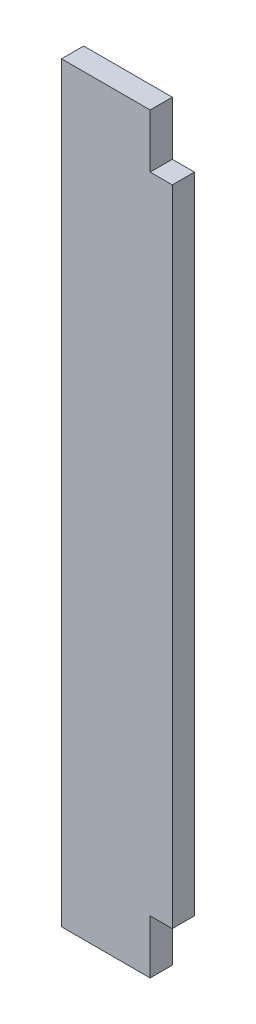
SolidWorks part; units mm, degrees
material "Pine"
ref_plane "Front Plane" through (0, 0, 0) normal (0, 0, 1) x (1, 0, 0)
ref_plane "Top Plane" through (0, 0, 0) normal (0, 1, 0) x (1, 0, 0)
ref_plane "Right Plane" through (0, 0, 0) normal (1, 0, 0) x (0, 0, -1)
sketch "Sketch1" plane through (0, 0, 0) normal (0, 0, 1) x (1, 0, 0)
  line L0 (8932.6508, -5243.5125) -> (10226.1458, -5243.5125)
  line L1 (9086.3208, -4722.0918) -> (10222.9708, -4853.7812)
  line L2 (8914.8708, -6342.0625) -> (10197.5708, -6342.0625)
  line L3 (8914.8708, -5808.6625) -> (10197.5708, -5808.6625)
  line L4 (8919.6333, -5253.0375) -> (10218.2083, -5253.0375)
  line L5 (9134.2633, -4656.1375) -> (9134.2633, -4638.3575)
  line L6 (9091.0833, -4638.3575) -> (9134.2633, -4638.3575)
  line L7 (9091.0833, -4567.2375) -> (9091.0833, -4638.3575)
  line L8 (9134.2633, -4656.1375) -> (9581.3033, -4656.1375)
  line L9 (9091.0833, -4567.2375) -> (9624.4833, -4567.2375)
  line L10 (9581.3033, -4656.1375) -> (9581.3033, -4638.3575)
  line L11 (9581.3033, -4638.3575) -> (9624.4833, -4638.3575)
  line L12 (9624.4833, -4567.2375) -> (9624.4833, -4638.3575)
  line L13 (8932.6508, -5225.7325) -> (9344.9775, -5225.7325)
  line L14 (8932.6508, -5256.2125) -> (8932.6508, -5243.5125)
  line L15 (8911.6958, -5256.2125) -> (8932.6508, -5256.2125)
  line L16 (8914.8708, -4722.0918) -> (9086.3208, -4722.0918)
  line L17 (8911.6958, -4715.5913) -> (8932.6508, -4715.5913)
  line L18 (8914.8708, -6342.0625) -> (8914.8708, -5808.6625)
  line L19 (12082.9917, -4722.0918) -> (10946.3417, -4853.7812)
  line L20 (12236.6617, -5243.5125) -> (10943.1667, -5243.5125)
  line L21 (10951.1042, -5253.0375) -> (12249.6792, -5253.0375)
  line L22 (10838.3917, -5656.2625) -> (11308.2917, -5656.2625)
  line L23 (10838.3917, -5719.7625) -> (11308.2917, -5719.7625)
  line L24 (10838.3917, -5742.5368) -> (11308.2917, -5742.5368)
  line L25 (10806.6417, -6342.0625) -> (11340.0417, -6342.0625)
  line L26 (10803.4667, -6335.7125) -> (11343.2167, -6335.7125)
  line L27 (10803.4667, -6317.9325) -> (11343.2167, -6317.9325)
  line L28 (10943.1667, -5225.7325) -> (11376.4483, -5225.7325)
  line L29 (11506.7292, -4754.5625) -> (10806.6417, -4827.5875)
  line L30 (11506.7292, -4567.2375) -> (11506.7292, -4754.5625)
  line L31 (10806.6417, -4567.2375) -> (10806.6417, -4827.5875)
  line L32 (10806.6417, -4567.2375) -> (11506.7292, -4567.2375)
  line L33 (10235.6708, -6329.3625) -> (10245.1958, -6329.3625)
  line L34 (10245.1958, -6329.3625) -> (10254.7208, -6278.5625)
  line L35 (10302.3458, -6329.3625) -> (10311.8708, -6278.5625)
  line L36 (10302.3458, -6329.3625) -> (10292.8208, -6329.3625)
  line L37 (10245.1958, -5821.3625) -> (10254.7208, -5872.1625)
  line L38 (10235.6708, -5821.3625) -> (10245.1958, -5821.3625)
  line L39 (10292.8208, -5821.3625) -> (10302.3458, -5821.3625)
  line L40 (10302.3458, -5821.3625) -> (10311.8708, -5872.1625)
  line L41 (10235.6708, -5821.3625) -> (10235.6708, -6329.3625)
  line L42 (10254.7208, -5872.1625) -> (10254.7208, -6278.5625)
  line L43 (10311.8708, -5872.1625) -> (10311.8708, -6278.5625)
  line L44 (10292.8208, -5821.3625) -> (10292.8208, -6329.3625)
  line L45 (8932.6508, -5225.7325) -> (8932.6508, -4715.5913)
  line L46 (8911.6958, -4715.5913) -> (8911.6958, -5256.2125)
  line L47 (8914.8708, -5248.275) -> (8914.8708, -4722.0918)
  line L48 (8919.6333, -5253.0375) -> (8914.8708, -5248.275)
  line L49 (8914.8708, -5145.0875) -> (8937.426, -5145.0875)
  line L50 (8914.8708, -5202.2375) -> (8937.426, -5202.2375)
  line L51 (10838.3917, -5656.2625) -> (10838.3917, -5719.7625)
  line L52 (10832.0417, -5736.1868) -> (10856.1717, -5736.1868)
  line L53 (10806.6417, -6342.0625) -> (10806.6417, -5818.7368)
  line L54 (10832.0417, -5649.9125) -> (10856.1717, -5649.9125)
  line L55 (10832.0417, -5726.1125) -> (10856.1717, -5726.1125)
  line L56 (10806.6417, -5818.7368) -> (10833.9015, -5818.7368)
  line L57 (10832.0417, -5806.0442) -> (10851.6815, -5806.0442)
  line L58 (10856.1717, -5801.5541) -> (10856.1717, -5736.1868)
  line L59 (10838.3917, -5814.2467) -> (10838.3917, -5742.5368)
  line L60 (10832.0417, -5806.0442) -> (10832.0417, -5736.1868)
  line L61 (10803.4667, -6317.9325) -> (10803.4667, -6335.7125)
  line L62 (10197.5708, -5808.6625) -> (10197.5708, -6342.0625)
  line L63 (9762.3842, -6348.4125) -> (9762.3842, -5802.3125)
  line L64 (9780.1642, -6348.4125) -> (9762.3842, -6348.4125)
  line L65 (9780.1642, -5802.3125) -> (9780.1642, -6348.4125)
  line L66 (9762.3842, -5802.3125) -> (9780.1642, -5802.3125)
  line L67 (9332.2775, -6348.4125) -> (9332.2775, -5802.3125)
  line L68 (9332.2775, -6348.4125) -> (9350.0575, -6348.4125)
  line L69 (9350.0575, -5802.3125) -> (9350.0575, -6348.4125)
  line L70 (9332.2775, -5802.3125) -> (9350.0575, -5802.3125)
  line L71 (9993.8374, -6061.075) -> (9993.8374, -6045.2418)
  line L72 (9998.5999, -6065.8375) -> (10014.4331, -6065.8375)
  line L73 (9998.5999, -6084.8875) -> (10014.4331, -6084.8875)
  line L74 (9993.8374, -6105.4832) -> (9993.8374, -6089.65)
  line L75 (9974.7874, -6105.4832) -> (9974.7874, -6089.65)
  line L76 (9954.1917, -6084.8875) -> (9970.0249, -6084.8875)
  line L77 (9974.7874, -6061.075) -> (9974.7874, -6045.2418)
  line L78 (9954.1917, -6065.8375) -> (9970.0249, -6065.8375)
  line L79 (10793.9417, -6237.2875) -> (10816.4969, -6237.2875)
  line L80 (10793.9417, -6294.4375) -> (10816.4969, -6294.4375)
  line L81 (10856.1717, -5649.9125) -> (10856.1717, -5726.1125)
  line L82 (10832.0417, -5726.1125) -> (10832.0417, -5649.9125)
  line L83 (10226.1458, -5225.7325) -> (10226.1458, -5243.5125)
  line L84 (10205.1908, -5257.8) -> (10205.1908, -4844.2499)
  line L85 (10230.9083, -4844.2499) -> (10230.9083, -5257.8)
  line L86 (10205.1908, -5257.8) -> (10230.9083, -5257.8)
  line L87 (10205.1908, -4844.2499) -> (10230.9083, -4844.2499)
  line L88 (10946.3417, -5176.8375) -> (10968.8969, -5176.8375)
  line L89 (9349.4676, -5141.9125) -> (9358.2674, -5141.9125)
  line L90 (10946.3417, -5119.6875) -> (10968.8969, -5119.6875)
  line L91 (9929.011, -4660.9635) -> (10066.0807, -4660.9635)
  line L92 (9929.011, -4678.7435) -> (10066.0807, -4678.7435)
  line L93 (10943.1667, -5225.7325) -> (10943.1667, -5243.5125)
  line L94 (10946.3417, -5248.275) -> (10951.1042, -5253.0375)
  line L95 (10946.3417, -5257.8063) -> (10946.3417, -4849.0188)
  line L96 (10964.1217, -5257.8) -> (10964.1217, -4844.2499)
  line L97 (10938.4042, -4844.2499) -> (10938.4042, -5257.8)
  line L98 (10938.4042, -5257.8) -> (10964.1217, -5257.8)
  line L99 (10964.1217, -4844.2499) -> (10938.4042, -4844.2499)
  line L100 (10344.8908, -4560.8875) -> (10369.0208, -4560.8875)
  line L101 (10344.8908, -4560.8875) -> (10369.0208, -4560.8875)
  line L102 (10800.2917, -4560.8875) -> (10824.4217, -4560.8875)
  line L103 (10200.4156, -5119.6875) -> (10222.9708, -5119.6875)
  line L104 (10200.4156, -5176.8375) -> (10222.9708, -5176.8375)
  line L105 (9344.9775, -5146.4026) -> (9344.9775, -5225.7325)
  line L106 (10344.8908, -4560.8875) -> (10344.8908, -4833.9375)
  line L107 (9792.8642, -5225.7325) -> (9792.8642, -5146.4026)
  line L108 (9362.7575, -5225.7325) -> (9775.0842, -5225.7325)
  line L109 (9680.3633, -4761.8396) -> (9680.3633, -4559.9604)
  line L110 (9656.2333, -4559.9604) -> (9680.3633, -4559.9604)
  line L111 (9656.2333, -4761.8396) -> (9680.3633, -4761.8396)
  line L112 (9656.2333, -4761.8396) -> (9656.2333, -4559.9604)
  line L113 (9779.5743, -5141.9125) -> (9788.374, -5141.9125)
  line L114 (10070.5708, -4665.4536) -> (10070.5708, -4674.2534)
  line L115 (9924.5208, -4674.2534) -> (9924.5208, -4665.4536)
  line L116 (12127.4417, -6188.3925) -> (12205.5015, -6188.3925)
  line L117 (12209.9917, -6170.6125) -> (12209.9917, -6183.9024)
  line L118 (9792.8642, -5225.7325) -> (10226.1458, -5225.7325)
  line L119 (9662.5833, -4754.5625) -> (10362.6708, -4827.5875)
  line L120 (9662.5833, -4567.2375) -> (9662.5833, -4754.5625)
  line L121 (10362.6708, -4567.2375) -> (10362.6708, -4827.5875)
  line L122 (9662.5833, -4567.2375) -> (10362.6708, -4567.2375)
  line L123 (10824.4217, -4833.9375) -> (10800.2917, -4833.9375)
  line L124 (10800.2917, -4833.9375) -> (10800.2917, -4560.8875)
  line L125 (10824.4217, -4560.8875) -> (10824.4217, -4833.9375)
  line L126 (10344.8908, -4833.9375) -> (10369.0208, -4833.9375)
  line L127 (10369.0208, -4833.9375) -> (10369.0208, -4560.8875)
  line L128 (10222.9708, -5248.275) -> (10218.2083, -5253.0375)
  line L129 (10222.9708, -5257.8063) -> (10222.9708, -4849.0188)
  line L130 (11734.6544, -5701.375) -> (11739.2301, -5701.375)
  line L131 (9362.7575, -5225.7325) -> (9362.7575, -5146.4026)
  line L132 (9775.0842, -5146.4026) -> (9775.0842, -5225.7325)
  line L133 (11761.3864, -5701.375) -> (11756.8282, -5701.375)
  line L134 (11734.6544, -5693.755) -> (11739.2301, -5693.755)
  line L135 (11761.4039, -5693.755) -> (11756.8282, -5693.755)
  line L136 (11734.6544, -5701.375) -> (11739.2301, -5701.375)
  line L137 (11744.3462, -5721.3024) -> (11744.3462, -5706.4179)
  line L138 (11751.7122, -5721.3024) -> (11751.7122, -5706.4179)
  line L139 (11740.0917, -6170.6125) -> (11740.0917, -6183.9024)
  line L140 (11689.2917, -6188.3925) -> (11822.6417, -6188.3925)
  line L141 (11689.2917, -6348.4093) -> (11689.2917, -6164.2657)
  line L142 (11689.2917, -6164.2657) -> (11746.4417, -6164.2657)
  line L143 (11746.4417, -6164.2657) -> (11746.4417, -6188.3925)
  line L144 (11689.2917, -6164.2657) -> (11746.4417, -6164.2657)
  line L145 (11340.0417, -5818.7368) -> (11340.0417, -6342.0625)
  line L146 (11290.5117, -5726.1125) -> (11314.6417, -5726.1125)
  line L147 (11290.5117, -5649.9125) -> (11290.5117, -5726.1125)
  line L148 (11340.0417, -5818.7368) -> (11312.7818, -5818.7368)
  line L149 (11314.6417, -5806.0442) -> (11295.0018, -5806.0442)
  line L150 (11290.5117, -5801.5541) -> (11290.5117, -5736.1868)
  line L151 (11308.2917, -5814.2467) -> (11308.2917, -5742.5368)
  line L152 (11314.6417, -5806.0442) -> (11314.6417, -5736.1868)
  line L153 (11290.5117, -5736.1868) -> (11314.6417, -5736.1868)
  line L154 (11848.0417, -6267.1325) -> (11962.3417, -6267.1325)
  line L155 (11962.3417, -6267.1325) -> (11962.3417, -6203.6325)
  line L156 (11343.2167, -6317.9325) -> (11343.2167, -6335.7125)
  line L157 (11365.4417, -5656.2625) -> (11365.4417, -5719.7625)
  line L158 (11365.4417, -5656.2625) -> (11479.7417, -5656.2625)
  line L159 (11778.1917, -6071.3937) -> (11802.3217, -6071.3937)
  line L160 (11314.6417, -5726.1125) -> (11314.6417, -5649.9125)
  line L161 (11314.6417, -5649.9125) -> (11290.5117, -5649.9125)
  line L162 (11308.2917, -5719.7625) -> (11308.2917, -5656.2625)
  line L163 (11689.2917, -6348.4093) -> (11713.4217, -6348.4093)
  line L164 (12203.6417, -6164.2657) -> (12260.7917, -6164.2657)
  line L165 (11713.4217, -6348.4093) -> (11713.4217, -6164.2657)
  line L166 (11695.6417, -6342.0625) -> (11695.6417, -6170.6125)
  line L167 (11695.6417, -6048.5337) -> (11699.4517, -6052.3437)
  line L168 (11822.6417, -6292.5325) -> (11822.6417, -6188.3925)
  line L169 (11695.6417, -6342.0625) -> (11695.6417, -6170.6125)
  line L170 (11848.0417, -6203.6325) -> (11962.3417, -6203.6325)
  line L171 (11848.0417, -6203.6325) -> (11848.0417, -6267.1325)
  line L172 (11987.7417, -6267.1325) -> (11987.7417, -6203.6325)
  line L173 (11784.5417, -6077.7437) -> (11784.5417, -6141.2438)
  line L174 (11517.8417, -5656.2625) -> (11632.1417, -5656.2625)
  line L175 (11632.1417, -5656.2625) -> (11632.1417, -5719.7625)
  line L176 (11632.1417, -5719.7625) -> (11517.8417, -5719.7625)
  line L177 (11517.8417, -5719.7625) -> (11517.8417, -5656.2625)
  line L178 (11692.4667, -6028.2137) -> (11692.4667, -6045.9937)
  line L179 (11695.6417, -5979.3188) -> (11718.1969, -5979.3188)
  line L180 (11695.6417, -5922.1687) -> (11718.1969, -5922.1687)
  line L181 (11821.0415, -5722.9375) -> (11821.0415, -5943.6)
  line L182 (11687.7042, -5651.5) -> (11701.9917, -5651.5)
  line L183 (11687.7042, -5651.5) -> (11687.7042, -6055.5251)
  line L184 (11687.7042, -6055.5251) -> (11701.9917, -6055.5251)
  line L185 (11701.9917, -6055.5251) -> (11701.9917, -5651.5)
  line L186 (11695.6417, -6055.2013) -> (11695.6417, -5649.595)
  line L187 (11695.6417, -5656.2625) -> (11695.6417, -6048.5337)
  line L188 (11695.6417, -6170.6125) -> (11740.0917, -6170.6125)
  line L189 (12203.6417, -6164.2657) -> (12203.6417, -6188.3925)
  line L190 (12254.4417, -6342.0625) -> (12254.4417, -6170.6125)
  line L191 (12129.0419, -5943.6) -> (12129.0419, -5722.9375)
  line L192 (12254.4417, -6048.5337) -> (12250.6317, -6052.3437)
  line L193 (12257.6167, -6045.9937) -> (12257.6167, -6028.2137)
  line L194 (12248.0917, -5651.5) -> (12262.3792, -5651.5)
  line L195 (12262.3792, -5651.5) -> (12262.3792, -6055.5251)
  line L196 (12262.3792, -6055.5251) -> (12248.0917, -6055.5251)
  line L197 (12248.0917, -6055.5251) -> (12248.0917, -5651.5)
  line L198 (12254.4417, -6141.2438) -> (12254.4417, -6077.7437)
  line L199 (12236.6617, -6164.2657) -> (12260.7917, -6164.2657)
  line L200 (12102.0417, -6267.1325) -> (11987.7417, -6267.1325)
  line L201 (11330.1865, -6237.2875) -> (11352.7417, -6237.2875)
  line L202 (11330.1865, -6294.4375) -> (11352.7417, -6294.4375)
  line L203 (11474.6617, -5851.8425) -> (11492.4417, -5851.8425)
  line L204 (11474.6617, -5808.6625) -> (11474.6617, -5851.8425)
  line L205 (11403.5417, -5808.6625) -> (11474.6617, -5808.6625)
  line L206 (11492.4417, -5851.8425) -> (11492.4417, -6298.8825)
  line L207 (11403.5417, -6342.0625) -> (11403.5417, -5808.6625)
  line L208 (11474.6617, -6298.8825) -> (11492.4417, -6298.8825)
  line L209 (11474.6617, -6342.0625) -> (11474.6617, -6298.8825)
  line L210 (11403.5417, -6342.0625) -> (11474.6617, -6342.0625)
  line L211 (11619.4417, -5851.8425) -> (11601.6617, -5851.8425)
  line L212 (11601.6617, -5808.6625) -> (11601.6617, -5851.8425)
  line L213 (11530.5417, -5808.6625) -> (11601.6617, -5808.6625)
  line L214 (11619.4417, -5851.8425) -> (11619.4417, -6298.8825)
  line L215 (11530.5417, -6342.0625) -> (11530.5417, -5808.6625)
  line L216 (11619.4417, -6298.8825) -> (11601.6617, -6298.8825)
  line L217 (11601.6617, -6342.0625) -> (11601.6617, -6298.8825)
  line L218 (11530.5417, -6342.0625) -> (11601.6617, -6342.0625)
  line L219 (11479.7417, -5719.7625) -> (11479.7417, -5656.2625)
  line L220 (11365.4417, -5719.7625) -> (11479.7417, -5719.7625)
  line L221 (11778.1917, -6147.5937) -> (11802.3217, -6147.5937)
  line L222 (11802.3217, -6071.3937) -> (11802.3217, -6147.5937)
  line L223 (11778.1917, -6147.5937) -> (11778.1917, -6071.3937)
  line L224 (12254.4417, -5922.1687) -> (12231.8865, -5922.1687)
  line L225 (12254.4417, -5979.3188) -> (12231.8865, -5979.3188)
  line L226 (12254.4417, -6055.2013) -> (12254.4417, -5649.595)
  line L227 (12254.4417, -6048.5337) -> (12254.4417, -5656.2625)
  line L228 (11841.6917, -5702.2873) -> (12108.3917, -5702.2873)
  line L229 (11822.6417, -6292.5325) -> (12127.4417, -6292.5325)
  line L230 (12127.4417, -6292.5325) -> (12127.4417, -6188.3925)
  line L231 (12254.4417, -6170.6125) -> (12209.9917, -6170.6125)
  line L232 (11695.6417, -6342.0625) -> (12254.4417, -6342.0625)
  line L233 (12236.6617, -6348.4093) -> (12260.7917, -6348.4093)
  line L234 (12260.7917, -6348.4093) -> (12260.7917, -6164.2657)
  line L235 (12236.6617, -6348.4093) -> (12236.6617, -6164.2657)
  line L236 (12102.0417, -6203.6325) -> (12102.0417, -6267.1325)
  line L237 (11987.7417, -6203.6325) -> (12102.0417, -6203.6325)
  line L238 (12236.6617, -6147.5937) -> (12236.6617, -6071.3937)
  line L239 (12203.6417, -6188.3925) -> (12260.7917, -6188.3925)
  line L240 (11098.7417, -4665.4536) -> (11098.7417, -4674.2534)
  line L241 (11394.2283, -5146.4026) -> (11394.2283, -5225.7325)
  line L242 (11376.4483, -5225.7325) -> (11376.4483, -5146.4026)
  line L243 (11394.2283, -5225.7325) -> (11806.555, -5225.7325)
  line L244 (11841.6917, -5964.2502) -> (12108.3917, -5964.2502)
  line L245 (12236.6617, -6147.5937) -> (12260.7917, -6147.5937)
  line L246 (12236.6617, -5256.2125) -> (12236.6617, -5243.5125)
  line L247 (12260.7917, -6147.5937) -> (12260.7917, -6071.3937)
  line L248 (12260.7917, -6071.3937) -> (12236.6617, -6071.3937)
  line L249 (12254.4417, -6077.7437) -> (11784.5417, -6077.7437)
  line L250 (11784.5417, -6141.2438) -> (12254.4417, -6141.2438)
  line L252 (12254.4417, -5656.2625) -> (11695.6417, -5656.2625)
  line L253 (11699.4517, -6052.3437) -> (12250.6317, -6052.3437)
  line L254 (11692.4667, -6045.9937) -> (12257.6167, -6045.9937)
  line L255 (11692.4667, -6028.2137) -> (12257.6167, -6028.2137)
  line L256 (11824.335, -5146.4026) -> (11824.335, -5225.7325)
  line L257 (11811.0451, -5141.9125) -> (11819.8449, -5141.9125)
  line L258 (11244.7917, -4674.2534) -> (11244.7917, -4665.4536)
  line L259 (11806.555, -5225.7325) -> (11806.555, -5146.4026)
  line L260 (11488.9492, -4761.8396) -> (11488.9492, -4559.9604)
  line L261 (11488.9492, -4559.9604) -> (11513.0792, -4559.9604)
  line L262 (11488.9492, -4761.8396) -> (11513.0792, -4761.8396)
  line L263 (11513.0792, -4761.8396) -> (11513.0792, -4559.9604)
  line L264 (11240.3015, -4660.9635) -> (11103.2318, -4660.9635)
  line L265 (11103.2318, -4678.7435) -> (11240.3015, -4678.7435)
  line L266 (12236.6617, -5225.7325) -> (12236.6617, -4715.5913)
  line L267 (12257.6167, -4715.5913) -> (12257.6167, -5256.2125)
  line L268 (12254.4417, -5248.275) -> (12254.4417, -4722.0918)
  line L269 (12236.6617, -5225.7325) -> (11824.335, -5225.7325)
  line L270 (12035.0492, -4656.1375) -> (12035.0492, -4638.3575)
  line L271 (12078.2292, -4638.3575) -> (12035.0492, -4638.3575)
  line L272 (12078.2292, -4567.2375) -> (12078.2292, -4638.3575)
  line L273 (12035.0492, -4656.1375) -> (11588.0092, -4656.1375)
  line L274 (11544.8292, -4567.2375) -> (12078.2292, -4567.2375)
  line L275 (11588.0092, -4656.1375) -> (11588.0092, -4638.3575)
  line L276 (11544.8292, -4638.3575) -> (11588.0092, -4638.3575)
  line L277 (11544.8292, -4567.2375) -> (11544.8292, -4638.3575)
  line L278 (12249.6792, -5253.0375) -> (12254.4417, -5248.275)
  line L280 (12257.6167, -5256.2125) -> (12236.6617, -5256.2125)
  line L281 (12231.8865, -5145.0875) -> (12254.4417, -5145.0875)
  line L282 (12231.8865, -5202.2375) -> (12254.4417, -5202.2375)
  line L283 (12236.6617, -4715.5913) -> (12257.6167, -4715.5913)
  line L284 (12082.9917, -4722.0918) -> (12254.4417, -4722.0918)
  line L285 (11380.9385, -5141.9125) -> (11389.7382, -5141.9125)
  circle A0 centre (8923.7608, -4778.9042) radius 1.5875
  circle A1 centre (9062.6598, -4736.3765) radius 2.3685
  circle A2 centre (9051.3958, -6281.7375) radius 22.225
  circle A3 centre (9083.1458, -6249.9875) radius 1.5875
  circle A4 centre (9083.1458, -6313.4875) radius 1.5875
  circle A5 centre (9019.6458, -6249.9875) radius 1.5875
  circle A6 centre (9019.6458, -6313.4875) radius 1.5875
  circle A7 centre (8972.3383, -5202.2375) radius 1.5875
  circle A8 centre (8923.7608, -5015.9708) radius 1.5875
  circle A9 centre (8923.7608, -5134.5042) radius 1.5875
  circle A10 centre (9054.5708, -5234.6225) radius 1.5875
  circle A11 centre (8923.7608, -4897.4375) radius 1.5875
  circle A12 centre (8972.3383, -5087.9375) radius 1.5875
  circle A13 centre (8972.3383, -5145.0875) radius 1.5875
  circle A14 centre (10847.2817, -5668.9625) radius 1.5875
  circle A15 centre (10847.2817, -5707.0625) radius 1.5875
  circle A16 centre (10847.2817, -5755.2368) radius 1.5875
  circle A17 centre (10851.4092, -6237.2875) radius 1.5875
  circle A18 centre (10851.4092, -6294.4375) radius 1.5875
  circle A19 centre (10847.2817, -5793.3442) radius 1.5875
  arc A20 (10833.9015, -5818.7368) -> (10838.3917, -5814.2467) centre (10836.1466, -5816.4918) ccw
  arc A21 (10851.6815, -5806.0442) -> (10856.1717, -5801.5541) centre (10853.9266, -5803.7992) ccw
  circle A22 centre (10882.8417, -6040.4375) radius 1.5875
  circle A23 centre (10882.8417, -6218.2375) radius 1.5875
  circle A24 centre (10882.8417, -5862.6375) radius 1.5875
  circle A25 centre (10908.2417, -6326.8225) radius 1.5875
  circle A26 centre (10908.2417, -6326.8225) radius 1.5875
  circle A27 centre (10851.4092, -6180.1375) radius 1.5875
  circle A28 centre (10815.5317, -4783.4231) radius 1.5875
  circle A29 centre (10815.5317, -4696.9488) radius 1.5875
  circle A30 centre (10815.5317, -4610.4746) radius 1.5875
  circle A31 centre (10979.1323, -4867.0082) radius 2.3685
  circle A32 centre (10190.1802, -4867.0082) radius 2.3685
  circle A33 centre (10955.2317, -4929.9812) radius 1.5875
  circle A34 centre (10955.2317, -5031.5812) radius 1.5875
  circle A35 centre (10214.0808, -4929.9812) radius 1.5875
  circle A36 centre (10214.0808, -5031.5812) radius 1.5875
  circle A37 centre (9341.1675, -6265.8625) radius 1.5875
  circle A38 centre (9771.2742, -5884.8625) radius 1.5875
  circle A39 centre (9771.2742, -6138.8625) radius 1.5875
  circle A40 centre (9771.2742, -6011.8625) radius 1.5875
  arc A41 (10036.2287, -6113.8083) -> (10051.3426, -6111.6033) centre (10042.9639, -6107.0732) ccw
  arc A42 (10051.3426, -6111.6033) -> (10051.3426, -6039.1217) centre (9984.3124, -6075.3625) ccw
  arc A43 (10051.3426, -6039.1217) -> (10036.2287, -6036.9167) centre (10042.9639, -6043.6518) ccw
  arc A44 (10034.5851, -6102.5431) -> (10034.5851, -6048.1819) centre (9984.3124, -6075.3625) ccw
  arc A45 (10034.5851, -6102.5431) -> (10036.2287, -6113.8083) centre (10042.9639, -6107.0732) ccw
  arc A46 (10036.2287, -6036.9167) -> (10034.5851, -6048.1819) centre (10042.9639, -6043.6518) ccw
  arc A47 (9945.8666, -6127.2787) -> (9948.0717, -6142.3927) centre (9952.6018, -6134.0139) ccw
  arc A48 (9948.0717, -6142.3927) -> (10020.5532, -6142.3927) centre (9984.3124, -6075.3625) ccw
  arc A49 (10020.5532, -6142.3927) -> (10022.7583, -6127.2787) centre (10016.0231, -6134.0139) ccw
  arc A50 (9957.1319, -6125.6352) -> (10011.493, -6125.6352) centre (9984.3124, -6075.3625) ccw
  arc A51 (9957.1319, -6125.6352) -> (9945.8666, -6127.2787) centre (9952.6018, -6134.0139) ccw
  arc A52 (10022.7583, -6127.2787) -> (10011.493, -6125.6352) centre (10016.0231, -6134.0139) ccw
  arc A53 (9932.3962, -6036.9167) -> (9917.2822, -6039.1217) centre (9925.661, -6043.6518) ccw
  arc A54 (9917.2822, -6039.1217) -> (9917.2822, -6111.6033) centre (9984.3124, -6075.3625) ccw
  arc A55 (9917.2822, -6111.6033) -> (9932.3962, -6113.8083) centre (9925.661, -6107.0732) ccw
  arc A56 (9934.0398, -6048.1819) -> (9934.0398, -6102.5431) centre (9984.3124, -6075.3625) ccw
  arc A57 (9934.0398, -6048.1819) -> (9932.3962, -6036.9167) centre (9925.661, -6043.6518) ccw
  arc A58 (9932.3962, -6113.8083) -> (9934.0398, -6102.5431) centre (9925.661, -6107.0732) ccw
  arc A59 (9945.8666, -6023.4463) -> (9957.1319, -6025.0898) centre (9952.6018, -6016.7111) ccw
  arc A60 (10011.493, -6025.0898) -> (10022.7583, -6023.4463) centre (10016.0231, -6016.7111) ccw
  arc A61 (10011.493, -6025.0898) -> (9957.1319, -6025.0898) centre (9984.3124, -6075.3625) ccw
  arc A62 (9948.0717, -6008.3323) -> (9945.8666, -6023.4463) centre (9952.6018, -6016.7111) ccw
  arc A63 (10020.5532, -6008.3323) -> (9948.0717, -6008.3323) centre (9984.3124, -6075.3625) ccw
  arc A64 (10022.7583, -6023.4463) -> (10020.5532, -6008.3323) centre (10016.0231, -6016.7111) ccw
  arc A65 (10005.0943, -6187.7574) -> (10096.7073, -6096.1443) centre (9984.3124, -6075.3625) ccw
  arc A66 (9993.8374, -6178.3911) -> (10005.0943, -6187.7574) centre (10003.3624, -6178.3911) ccw
  arc A67 (10001.6306, -6169.0249) -> (10077.9748, -6092.6807) centre (9984.3124, -6075.3625) ccw
  arc A68 (10087.3411, -6084.8875) -> (10077.9748, -6092.6807) centre (10087.3411, -6094.4125) ccw
  arc A69 (10001.6306, -6169.0249) -> (9993.8374, -6178.3911) centre (10003.3624, -6178.3911) ccw
  arc A70 (9963.5306, -6187.7574) -> (9974.7874, -6178.3911) centre (9965.2624, -6178.3911) ccw
  arc A71 (9871.9176, -6096.1443) -> (9963.5306, -6187.7574) centre (9984.3124, -6075.3625) ccw
  arc A72 (9881.2838, -6084.8875) -> (9871.9176, -6096.1443) centre (9881.2838, -6094.4125) ccw
  arc A73 (9890.65, -6092.6807) -> (9966.9943, -6169.0249) centre (9984.3124, -6075.3625) ccw
  arc A74 (9974.7874, -6178.3911) -> (9966.9943, -6169.0249) centre (9965.2624, -6178.3911) ccw
  arc A75 (9890.65, -6092.6807) -> (9881.2838, -6084.8875) centre (9881.2838, -6094.4125) ccw
  arc A76 (9871.9176, -6054.5807) -> (9881.2838, -6065.8375) centre (9881.2838, -6056.3125) ccw
  arc A77 (9963.5306, -5962.9676) -> (9871.9176, -6054.5807) centre (9984.3124, -6075.3625) ccw
  arc A78 (9974.7874, -5972.3339) -> (9963.5306, -5962.9676) centre (9965.2624, -5972.3339) ccw
  arc A79 (9966.9943, -5981.7001) -> (9890.65, -6058.0443) centre (9984.3124, -6075.3625) ccw
  arc A80 (9881.2838, -6065.8375) -> (9890.65, -6058.0443) centre (9881.2838, -6056.3125) ccw
  arc A81 (9966.9943, -5981.7001) -> (9974.7874, -5972.3339) centre (9965.2624, -5972.3339) ccw
  arc A82 (10077.9748, -6058.0443) -> (10087.3411, -6065.8375) centre (10087.3411, -6056.3125) ccw
  arc A83 (9993.8374, -5972.3339) -> (10001.6306, -5981.7001) centre (10003.3624, -5972.3339) ccw
  arc A84 (10077.9748, -6058.0443) -> (10001.6306, -5981.7001) centre (9984.3124, -6075.3625) ccw
  arc A85 (10087.3411, -6065.8375) -> (10096.7073, -6054.5807) centre (10087.3411, -6056.3125) ccw
  arc A86 (10096.7073, -6054.5807) -> (10005.0943, -5962.9676) centre (9984.3124, -6075.3625) ccw
  arc A87 (10005.0943, -5962.9676) -> (9993.8374, -5972.3339) centre (10003.3624, -5972.3339) ccw
  arc A88 (10014.4331, -6065.8375) -> (10018.7361, -6059.0339) centre (10014.4331, -6061.075) ccw
  arc A89 (10018.7361, -6059.0339) -> (10000.641, -6040.9388) centre (9984.3124, -6075.3625) ccw
  arc A90 (10000.641, -6040.9388) -> (9993.8374, -6045.2418) centre (9998.5999, -6045.2418) ccw
  arc A91 (9993.8374, -6061.075) -> (9998.5999, -6065.8375) centre (9998.5999, -6061.075) ccw
  arc A92 (9993.8374, -6105.4832) -> (10000.641, -6109.7862) centre (9998.5999, -6105.4832) ccw
  arc A93 (10000.641, -6109.7862) -> (10018.7361, -6091.6911) centre (9984.3124, -6075.3625) ccw
  arc A94 (10018.7361, -6091.6911) -> (10014.4331, -6084.8875) centre (10014.4331, -6089.65) ccw
  arc A95 (9998.5999, -6084.8875) -> (9993.8374, -6089.65) centre (9998.5999, -6089.65) ccw
  arc A96 (9954.1917, -6084.8875) -> (9949.8888, -6091.6911) centre (9954.1917, -6089.65) ccw
  arc A97 (9949.8888, -6091.6911) -> (9967.9839, -6109.7862) centre (9984.3124, -6075.3625) ccw
  arc A98 (9967.9839, -6109.7862) -> (9974.7874, -6105.4832) centre (9970.0249, -6105.4832) ccw
  arc A99 (9974.7874, -6089.65) -> (9970.0249, -6084.8875) centre (9970.0249, -6089.65) ccw
  arc A100 (9970.0249, -6065.8375) -> (9974.7874, -6061.075) centre (9970.0249, -6061.075) ccw
  arc A101 (9949.8888, -6059.0339) -> (9954.1917, -6065.8375) centre (9954.1917, -6061.075) ccw
  arc A102 (9967.9839, -6040.9388) -> (9949.8888, -6059.0339) centre (9984.3124, -6075.3625) ccw
  arc A103 (9974.7874, -6045.2418) -> (9967.9839, -6040.9388) centre (9970.0249, -6045.2418) ccw
  arc A104 (10096.7073, -6096.1443) -> (10087.3411, -6084.8875) centre (10087.3411, -6094.4125) ccw
  circle A105 centre (9771.2742, -6265.8625) radius 1.5875
  circle A106 centre (9341.1675, -5884.8625) radius 1.5875
  circle A107 centre (9341.1675, -6138.8625) radius 1.5875
  circle A108 centre (9341.1675, -6011.8625) radius 1.5875
  circle A109 centre (11037.2315, -4887.5494) radius 15.0812
  arc A110 (9349.4676, -5141.9125) -> (9344.9775, -5146.4026) centre (9347.2226, -5144.1576) ccw
  arc A111 (9362.7575, -5146.4026) -> (9358.2674, -5141.9125) centre (9360.5124, -5144.1576) ccw
  circle A112 centre (9946.7458, -4669.8535) radius 1.5875
  arc A113 (9924.5208, -4674.2534) -> (9929.011, -4678.7435) centre (9926.7659, -4676.4984) ccw
  circle A114 centre (11003.8092, -5176.8375) radius 1.5875
  circle A115 centre (11003.8092, -5119.6875) radius 1.5875
  circle A116 centre (10353.7808, -4696.9488) radius 1.5875
  circle A117 centre (10353.7808, -4610.4746) radius 1.5875
  circle A118 centre (10353.7808, -4783.4231) radius 1.5875
  circle A119 centre (11003.8092, -5062.5375) radius 1.5875
  circle A120 centre (9353.8675, -5160.9625) radius 1.5875
  circle A121 centre (9638.7708, -5234.6225) radius 1.5875
  circle A122 centre (9671.4733, -4724.1144) radius 1.5875
  circle A123 centre (9671.4733, -4661.3637) radius 1.5875
  circle A124 centre (9671.4733, -4598.6129) radius 1.5875
  arc A125 (9792.8642, -5146.4026) -> (9788.374, -5141.9125) centre (9790.6191, -5144.1576) ccw
  arc A126 (9779.5743, -5141.9125) -> (9775.0842, -5146.4026) centre (9777.3292, -5144.1576) ccw
  circle A127 centre (10048.3458, -4669.8535) radius 1.5875
  arc A128 (10070.5708, -4665.4536) -> (10066.0807, -4660.9635) centre (10068.3258, -4663.2086) ccw
  arc A129 (10066.0807, -4678.7435) -> (10070.5708, -4674.2534) centre (10068.3258, -4676.4984) ccw
  circle A130 centre (9997.5458, -4669.8535) radius 1.5875
  arc A131 (9929.011, -4660.9635) -> (9924.5208, -4665.4536) centre (9926.7659, -4663.2086) ccw
  circle A132 centre (10132.081, -4887.5494) radius 15.0812
  circle A133 centre (10165.5033, -5176.8375) radius 1.5875
  circle A134 centre (10165.5033, -5119.6875) radius 1.5875
  circle A135 centre (9486.3708, -5234.6225) radius 1.5875
  circle A136 centre (10165.5033, -5062.5375) radius 1.5875
  circle A137 centre (9206.9708, -5234.6225) radius 1.5875
  circle A138 centre (10070.5708, -5234.6225) radius 1.5875
  circle A139 centre (9918.1708, -5234.6225) radius 1.5875
  circle A140 centre (9783.9742, -5160.9625) radius 1.5875
  circle A141 centre (9783.9742, -5193.9825) radius 1.5875
  circle A142 centre (9353.8675, -5193.9825) radius 1.5875
  circle A143 centre (11073.3417, -6326.8225) radius 1.5875
  circle A144 centre (11073.3417, -6326.8225) radius 1.5875
  circle A145 centre (11295.2742, -6180.1375) radius 1.5875
  circle A146 centre (11295.2742, -6294.4375) radius 1.5875
  circle A147 centre (11295.2742, -6237.2875) radius 1.5875
  circle A148 centre (11975.0417, -5692.775) radius 3.4925
  circle A149 centre (11263.8417, -5862.6375) radius 1.5875
  arc A150 (11739.2301, -5701.375) -> (11744.3462, -5706.4179) centre (11748.0292, -5697.565) ccw
  arc A151 (11751.7122, -5706.4179) -> (11756.8282, -5701.375) centre (11748.0292, -5697.565) ccw
  arc A152 (11744.3462, -5721.3024) -> (11751.7122, -5721.3024) centre (11748.0292, -5725.505) ccw
  arc A153 (11734.6544, -5693.755) -> (11724.9787, -5697.565) centre (11730.5667, -5697.565) ccw
  arc A154 (11756.8282, -5693.755) -> (11739.2301, -5693.755) centre (11748.0292, -5697.565) ccw
  arc A155 (11724.9787, -5697.565) -> (11734.6544, -5701.375) centre (11730.5667, -5697.565) ccw
  arc A156 (11761.3864, -5701.375) -> (11771.0797, -5697.565) centre (11765.4842, -5697.565) ccw
  arc A157 (11771.0797, -5697.565) -> (11761.4039, -5693.755) centre (11765.4917, -5697.565) ccw
  arc A158 (11740.0917, -6183.9024) -> (11744.5818, -6188.3925) centre (11742.3367, -6186.1474) ccw
  arc A159 (12205.5015, -6188.3925) -> (12209.9917, -6183.9024) centre (12207.7466, -6186.1474) ccw
  circle A160 centre (11299.4017, -5793.3442) radius 1.5875
  arc A161 (11308.2917, -5814.2467) -> (11312.7818, -5818.7368) centre (11310.5367, -5816.4918) ccw
  arc A162 (11290.5117, -5801.5541) -> (11295.0018, -5806.0442) centre (11292.7567, -5803.7992) ccw
  circle A163 centre (11704.5317, -6314.149) radius 1.5875
  circle A164 centre (11748.9817, -6208.7125) radius 1.5875
  circle A165 centre (11263.8417, -6218.2375) radius 1.5875
  circle A166 centre (11263.8417, -6040.4375) radius 1.5875
  circle A167 centre (11238.4417, -6326.8225) radius 1.5875
  circle A168 centre (11238.4417, -6326.8225) radius 1.5875
  circle A169 centre (11299.4017, -5668.9625) radius 1.5875
  circle A170 centre (11299.4017, -5707.0625) radius 1.5875
  circle A171 centre (11726.7567, -6179.5025) radius 1.5875
  circle A172 centre (11704.5317, -6199.3198) radius 1.5875
  circle A173 centre (11748.9817, -6272.2125) radius 1.5875
  circle A174 centre (11704.5317, -6256.7344) radius 1.5875
  circle A175 centre (11299.4017, -5755.2368) radius 1.5875
  circle A176 centre (11913.4467, -6301.4225) radius 1.5875
  circle A177 centre (11790.2567, -6301.4225) radius 1.5875
  circle A178 centre (11793.4317, -6128.5437) radius 1.5875
  circle A179 centre (11753.1092, -5865.0188) radius 1.5875
  circle A180 centre (11809.9417, -6037.1038) radius 1.5875
  circle A181 centre (11809.9417, -6037.1038) radius 1.5875
  circle A182 centre (11753.1092, -5922.1687) radius 1.5875
  circle A183 centre (11975.0417, -5973.7625) radius 3.4925
  circle A184 centre (11975.0417, -6037.1038) radius 1.5875
  circle A185 centre (11753.1092, -5979.3188) radius 1.5875
  circle A186 centre (11975.0417, -6037.1038) radius 1.5875
  arc A187 (11841.6917, -5702.2873) -> (11821.0415, -5722.9375) centre (11841.6917, -5722.9375) ccw
  circle A188 centre (11811.5292, -5833.2687) radius 3.4925
  arc A189 (11821.0415, -5943.6) -> (11841.6917, -5964.2502) centre (11841.6917, -5943.6) ccw
  circle A190 centre (12196.9742, -5865.0188) radius 1.5875
  arc A191 (12129.0419, -5722.9375) -> (12108.3917, -5702.2873) centre (12108.3917, -5722.9375) ccw
  circle A192 centre (12036.6367, -6301.4225) radius 1.5875
  circle A193 centre (12159.8267, -6301.4225) radius 1.5875
  circle A194 centre (12138.5542, -5833.2687) radius 3.4925
  circle A195 centre (12197.2917, -5761.0375) radius 15.0812
  circle A196 centre (11793.4317, -6090.4437) radius 1.5875
  circle A197 centre (12196.9742, -5922.1687) radius 1.5875
  arc A198 (12108.3917, -5964.2502) -> (12129.0419, -5943.6) centre (12108.3917, -5943.6) ccw
  circle A199 centre (12196.9742, -5979.3188) radius 1.5875
  circle A200 centre (12201.1017, -6272.2125) radius 1.5875
  circle A201 centre (12245.5517, -6314.149) radius 1.5875
  circle A202 centre (12245.5517, -6256.7344) radius 1.5875
  circle A203 centre (12201.1017, -6208.7125) radius 1.5875
  circle A204 centre (12223.3267, -6179.5025) radius 1.5875
  circle A205 centre (12245.5517, -6199.3198) radius 1.5875
  circle A206 centre (11171.7667, -4669.8535) radius 1.5875
  circle A207 centre (11222.5667, -4669.8535) radius 1.5875
  arc A208 (11240.3015, -4678.7435) -> (11244.7917, -4674.2534) centre (11242.5466, -4676.4984) ccw
  circle A209 centre (11385.3383, -5193.9825) radius 1.5875
  circle A210 centre (12106.6527, -4736.3765) radius 2.3685
  circle A211 centre (12140.1417, -6037.1038) radius 1.5875
  circle A212 centre (12140.1417, -6037.1038) radius 1.5875
  circle A213 centre (12245.5517, -6090.4437) radius 1.5875
  circle A214 centre (12245.5517, -6128.5437) radius 1.5875
  circle A215 centre (11385.3383, -5160.9625) radius 1.5875
  arc A216 (11824.335, -5146.4026) -> (11819.8449, -5141.9125) centre (11822.0899, -5144.1576) ccw
  arc A217 (11811.0451, -5141.9125) -> (11806.555, -5146.4026) centre (11808.8001, -5144.1576) ccw
  circle A218 centre (11815.445, -5193.9825) radius 1.5875
  circle A219 centre (11815.445, -5160.9625) radius 1.5875
  circle A220 centre (11530.5417, -5234.6225) radius 1.5875
  circle A221 centre (11962.3417, -5234.6225) radius 1.5875
  arc A222 (11244.7917, -4665.4536) -> (11240.3015, -4660.9635) centre (11242.5466, -4663.2086) ccw
  circle A223 centre (11682.9417, -5234.6225) radius 1.5875
  circle A224 centre (11497.8392, -4724.1144) radius 1.5875
  circle A225 centre (11497.8392, -4661.3637) radius 1.5875
  circle A226 centre (11497.8392, -4598.6129) radius 1.5875
  circle A227 centre (11120.9667, -4669.8535) radius 1.5875
  arc A228 (11103.2318, -4660.9635) -> (11098.7417, -4665.4536) centre (11100.9867, -4663.2086) ccw
  arc A229 (11098.7417, -4674.2534) -> (11103.2318, -4678.7435) centre (11100.9867, -4676.4984) ccw
  circle A230 centre (12196.9742, -5202.2375) radius 1.5875
  circle A231 centre (12245.5517, -5015.9708) radius 1.5875
  circle A232 centre (12245.5517, -5134.5042) radius 1.5875
  circle A233 centre (12114.7417, -5234.6225) radius 1.5875
  circle A234 centre (12245.5517, -4897.4375) radius 1.5875
  circle A235 centre (12245.5517, -4778.9042) radius 1.5875
  circle A236 centre (12196.9742, -5087.9375) radius 1.5875
  circle A237 centre (12196.9742, -5145.0875) radius 1.5875
  circle A238 centre (11098.7417, -5234.6225) radius 1.5875
  circle A239 centre (11251.1417, -5234.6225) radius 1.5875
  arc A240 (11380.9385, -5141.9125) -> (11376.4483, -5146.4026) centre (11378.6934, -5144.1576) ccw
  arc A241 (11394.2283, -5146.4026) -> (11389.7382, -5141.9125) centre (11391.9833, -5144.1576) ccw
sketch "BraceOutline" plane through (0, 0, 0) normal (0, 0, 1) x (1, 0, 0)
  line L0 (11403.5417, -6411.9125) -> (11474.6617, -6411.9125)
  line L1 (11474.6617, -6411.9125) -> (11474.6617, -6368.7325)
  line L2 (11474.6617, -6368.7325) -> (11492.4417, -6368.7325)
  line L3 (11492.4417, -6368.7325) -> (11492.4417, -5851.8425)
  line L4 (11492.4417, -5851.8425) -> (11474.6617, -5851.8425)
  line L5 (11474.6617, -5851.8425) -> (11474.6617, -5808.6625)
  line L6 (11474.6617, -5808.6625) -> (11403.5417, -5808.6625)
  line L7 (11403.5417, -5808.6625) -> (11403.5417, -6411.9125)
  dimension "Brace_Width" = 603.25
  dimension "Brace_GapWidth" = 43.18
  dimension "Brace_Height" = 88.9
  dimension "Brace_GapHeight" = 17.78
extrude "Brace_Thickness" add sketch "BraceOutline" against normal blind 17.78
